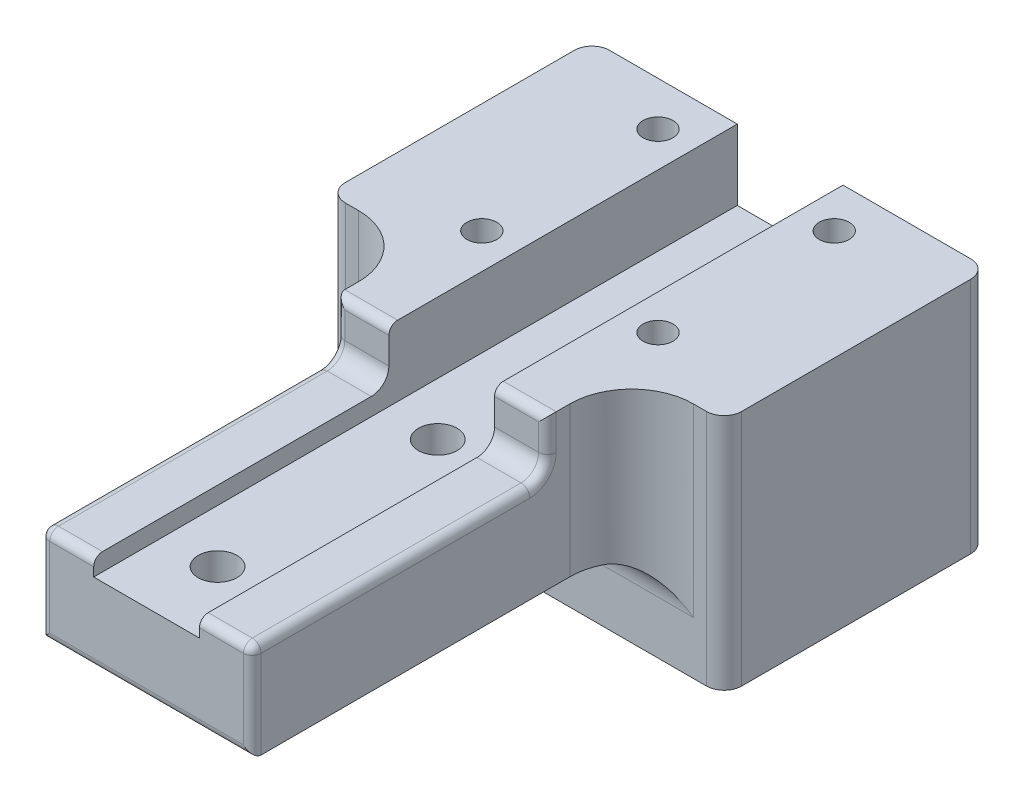
SolidWorks part; units mm, degrees
ref_plane "Front Plane" through (0, 0, 0) normal (0, 0, 1) x (1, 0, 0)
ref_plane "Top Plane" through (0, 0, 0) normal (0, 1, 0) x (1, 0, 0)
ref_plane "Right Plane" through (0, 0, 0) normal (1, 0, 0) x (0, 0, -1)
sketch "Sketch1" plane through (0, 0, 0) normal (0, 1, 0) x (1, 0, 0)
  line L0 (0, -55) -> (0, 55) construction
  line L1 (-22.5, 15) -> (22.5, 15)
  line L2 (-22.5, 15) -> (-22.5, -15)
  line L3 (-22.5, -15) -> (22.5, -15)
  line L4 (22.5, 15) -> (22.5, -15)
  line L5 (-22.5, 15) -> (22.5, -15) construction
  line L6 (-22.5, -15) -> (22.5, 15) construction
  line L7 (-10, 10) -> (10, 10)
  line L8 (-10, 10) -> (-10, -10) construction
  line L9 (-10, -10) -> (10, -10) construction
  line L10 (10, 10) -> (10, -10) construction
  line L11 (-10, 10) -> (10, -10) construction
  line L12 (-10, -10) -> (10, 10) construction
  line L13 (-12, -15) -> (12, -15)
  line L14 (-12, -15) -> (-12, -58.0584)
  line L15 (-12, -58.0584) -> (12, -58.0584)
  line L16 (12, -15) -> (12, -58.0584)
  line L17 (0, -1000) -> (0, 49000) construction
  circle A0 centre (-10, 10) radius 1.7
  circle A1 centre (10, 10) radius 1.7
  circle A2 centre (10, -10) radius 1.7
  circle A3 centre (-10, -10) radius 1.7
  circle A4 centre (0, -25) radius 2.2
  circle A5 centre (0, -50) radius 2.2
  point P0 (0, 0)
  point P6 (0, 0)
  dimension "D1" = 3.4
  dimension "D9" = 40
  dimension "D6" = 25
  dimension "D8" = 4.4
  dimension "D2" = 45
  dimension "D3" = 20
  dimension "D4" = 20
  dimension "D5" = 30
  dimension "D7" = 24
extrude "Boss-Extrude2" add sketch "Sketch1" against normal blind 17
sketch "Sketch5" plane through (0, 0, 0) normal (0, 1, 0) x (1, 0, 0)
  line L0 (0, -55) -> (0, 55) construction
  line L1 (-6, 33.5348) -> (6, 33.5348)
  line L2 (-6, 33.5348) -> (-6, -66.4652)
  line L3 (-6, -66.4652) -> (6, -66.4652)
  line L4 (6, 33.5348) -> (6, -66.4652)
  line L5 (-6, 33.5348) -> (6, -66.4652) construction
  line L6 (-6, -66.4652) -> (6, 33.5348) construction
  point P0 (0, -16.4652)
  dimension "D1" = 12
  dimension "D2" = 100
extrude "Cut-Extrude1" cut sketch "Sketch5" against normal blind 8
ref_plane "Plane12" through (0, -6, 0) normal (0, 1, 0) x (1, 0, 0)
sketch "Sketch7" plane through (0, -6, 0) normal (0, 1, 0) x (1, 0, 0)
  line L1 (-15.6584, -24.5529) -> (14.0386, -24.5529)
  line L2 (-15.6584, -24.5529) -> (-15.6584, -59.5414)
  line L3 (-15.6584, -59.5414) -> (14.0386, -59.5414)
  line L4 (14.0386, -24.5529) -> (14.0386, -59.5414)
  line L5 (-0.8099, -59.5414) -> (-0.8099, -24.5529) construction
  line L6 (-15.6584, -42.0471) -> (14.0386, -42.0471) construction
  point P192 (-0.8099, -42.0471)
extrude "Cut-Extrude2" cut sketch "Sketch7" along normal through all
sketch "Sketch9" plane through (0, -17, 0) normal (0, -1, 0) x (1, 0, 0)
  line L1 (-22.5, 15) -> (22.5, 15)
  line L2 (-22.5, 15) -> (-22.5, -15)
  line L3 (-22.5, -15) -> (22.5, -15)
  line L4 (22.5, 15) -> (22.5, -15)
  line L5 (0, -15) -> (0, 15) construction
  line L6 (-22.5, 0) -> (22.5, 0) construction
  point P232 (0, 0)
extrude "Boss-Extrude3" add sketch "Sketch9" along normal blind 10
fillet "Fillet1" radius 7 2 edges at (-12, -8.5, 15) (12, -8.5, 15)
fillet "Fillet6" radius 2 6 edges at (-9, -6, 24.5529) (9, -6, 24.5529) (-22.5, -13.5, 15) (-22.5, -13.5, -15) (22.5, -13.5, -15) (22.5, -13.5, 15)
fillet "Fillet7" radius 1 13 edges at (-12, -2, 24.5529) (-12, -5.4142, 25.1387) (12, -2, 24.5529) (12, -5.4142, 25.1387) (-12, -6, 42.3056) (-9, -6, 58.0584) (9, -6, 58.0584) (12, -6, 42.3056) (0, -17, 58.0584) (-12, -11.5, 58.0584) (12, -11.5, 58.0584) (-9, 0, 24.5529) (9, 0, 24.5529)
fillet "Fillet8" radius 4 1 edges at (0, -17, 15)
